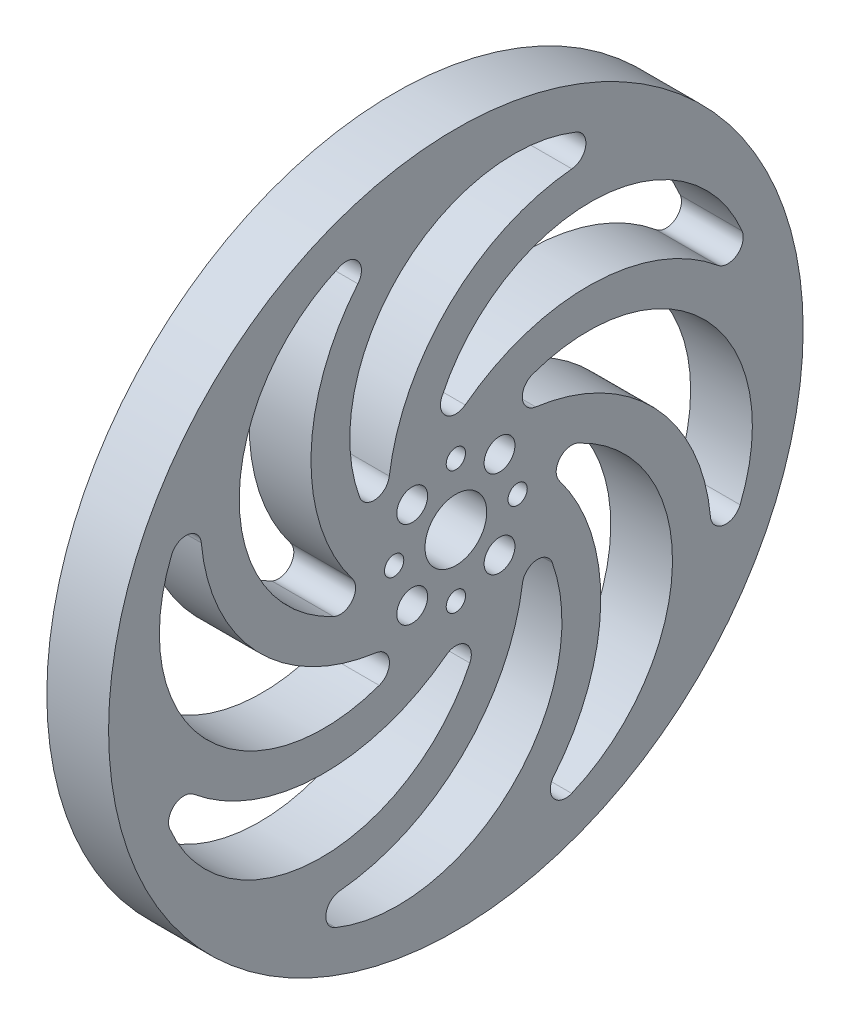
SolidWorks part; units mm, degrees
material "PMMA"
ref_plane "Front Plane" through (0, 0, 0) normal (0, 0, 1) x (1, 0, 0)
ref_plane "Top Plane" through (0, 0, 0) normal (0, 1, 0) x (1, 0, 0)
ref_plane "Right Plane" through (0, 0, 0) normal (1, 0, 0) x (0, 0, -1)
sketch "Sprocket" plane through (0, 0, 0) normal (1, 0, 0) x (0, 0, -1)
  circle A0 centre (0, 0) radius 45
  dimension "D1" = 90
extrude "Estrusione-Estrusione2" add sketch "Sprocket" along normal blind 8 contours A0
sketch "Schizzo1" plane through (0, 0, 0) normal (1, 0, 0) x (0, 0, -1)
  line L0 (0, 45) -> (0, -45) construction
  line L1 (31.8198, -31.8198) -> (-31.8198, 31.8198) construction
  line L2 (-31.8198, -31.8198) -> (31.8198, 31.8198) construction
  line L4 (-45, 0) -> (45, 0) construction
  circle A0 centre (0, 0) radius 4
  circle A1 centre (-5.6569, 5.6569) radius 2
  circle A2 centre (5.6569, 5.6569) radius 2
  circle A3 centre (0, 8) radius 1.25
  circle A4 centre (8, 0) radius 1.25
  circle A5 centre (-8, 0) radius 1.25
  circle A6 centre (0, -8) radius 1.25
  circle A7 centre (0, 0) radius 45 construction
  circle A8 centre (5.6569, -5.6569) radius 2
  circle A9 centre (-5.6569, -5.6569) radius 2
  point P5 (0, 0)
  point P8 (0, 0)
  point P15 (0, 0)
  point P16 (0, 0)
  point P36 (0, 0)
  dimension "D1" = 8
  dimension "D2" = 2.5
  dimension "D10" = 4
  dimension "D3" = 8
  dimension "D4" = 8
  dimension "D5" = 8
  dimension "D6" = 8
  dimension "D7" = 45
  dimension "D8" = 45
  dimension "D9" = 45
  dimension "D11" = 8
  dimension "D12" = 4
extrude "Taglio-Estrusione2" cut sketch "Schizzo1" along direction (1, 0, 0) on the side of the normal through all
sketch "Schizzo2" plane through (8, 0, 0) normal (1, 0, 0) x (0, 0, -1)
  line L0 (0, 0) -> (0, 15) construction
  line L1 (0, 0) -> (35.233, 14.2351) construction
  arc A0 (10.3368, 8.6249) -> (32.9876, -15.0314) centre (6.7868, -17.4465) cw
  arc A1 (32.9876, -15.0314) -> (36.8299, -15.606) centre (34.9792, -14.8478) ccw
  arc A2 (9.9294, 12.4885) -> (36.8299, -15.606) centre (17.1355, -7.5376) cw
  arc A3 (-1.8095, 15.8519) -> (1.2105, 13.4079) centre (0, 15) ccw
  arc A4 (33.9546, 12.697) -> (37.0778, 15.0076) centre (35.233, 14.2351) ccw
  circle A5 centre (0, 0) radius 15 construction
  circle A6 centre (0, 0) radius 38 construction
  circle A7 centre (0, 0) radius 45 construction
  arc A8 (1.2105, 13.4079) -> (33.9546, 12.697) centre (17.1355, -7.5376) cw
  arc A9 (9.9294, 12.4885) -> (10.3368, 8.6249) centre (10.6066, 10.6066) ccw
  arc A10 (13.4079, -1.2105) -> (12.697, -33.9546) centre (-7.5376, -17.1355) cw
  arc A11 (12.697, -33.9546) -> (15.0076, -37.0778) centre (14.2351, -35.233) ccw
  arc A12 (15.8519, 1.8095) -> (15.0076, -37.0778) centre (6.7868, -17.4465) cw
  arc A13 (15.8519, 1.8095) -> (13.4079, -1.2105) centre (15, 0) ccw
  arc A14 (8.6249, -10.3368) -> (-15.0314, -32.9876) centre (-17.4465, -6.7868) cw
  arc A15 (-15.0314, -32.9876) -> (-15.606, -36.8299) centre (-14.8478, -34.9792) ccw
  arc A16 (12.4885, -9.9294) -> (-15.606, -36.8299) centre (-7.5376, -17.1355) cw
  arc A17 (12.4885, -9.9294) -> (8.6249, -10.3368) centre (10.6066, -10.6066) ccw
  arc A18 (-1.8095, 15.8519) -> (37.0778, 15.0076) centre (17.4465, 6.7868) cw
  arc A19 (-1.2105, -13.4079) -> (-33.9546, -12.697) centre (-17.1355, 7.5376) cw
  arc A20 (-33.9546, -12.697) -> (-37.0778, -15.0076) centre (-35.233, -14.2351) ccw
  arc A21 (1.8095, -15.8519) -> (-37.0778, -15.0076) centre (-17.4465, -6.7868) cw
  arc A22 (1.8095, -15.8519) -> (-1.2105, -13.4079) centre (0, -15) ccw
  arc A23 (-10.3368, -8.6249) -> (-32.9876, 15.0314) centre (-6.7868, 17.4465) cw
  arc A24 (-32.9876, 15.0314) -> (-36.8299, 15.606) centre (-34.9792, 14.8478) ccw
  arc A25 (-9.9294, -12.4885) -> (-36.8299, 15.606) centre (-17.1355, 7.5376) cw
  arc A26 (-9.9294, -12.4885) -> (-10.3368, -8.6249) centre (-10.6066, -10.6066) ccw
  arc A27 (-13.4079, 1.2105) -> (-12.697, 33.9546) centre (7.5376, 17.1355) cw
  arc A28 (-12.697, 33.9546) -> (-15.0076, 37.0778) centre (-14.2351, 35.233) ccw
  arc A29 (-15.8519, -1.8095) -> (-15.0076, 37.0778) centre (-6.7868, 17.4465) cw
  arc A30 (-15.8519, -1.8095) -> (-13.4079, 1.2105) centre (-15, 0) ccw
  arc A31 (-8.6249, 10.3368) -> (15.0314, 32.9876) centre (17.4465, 6.7868) cw
  arc A32 (15.0314, 32.9876) -> (15.606, 36.8299) centre (14.8478, 34.9792) ccw
  arc A33 (-12.4885, 9.9294) -> (15.606, 36.8299) centre (7.5376, 17.1355) cw
  arc A34 (-12.4885, 9.9294) -> (-8.6249, 10.3368) centre (-10.6066, 10.6066) ccw
  point P41 (0, 0)
  point P50 (0, 0)
  point P76 (10.6066, 10.6066)
  point P90 (0, 0)
  dimension "D1" = 30
  dimension "D2" = 7
  dimension "D3" = 68
  dimension "D4" = 2
  dimension "D5" = 2
  dimension "D6" = 8
  dimension "D7" = 5.0289
extrude "Taglio-Estrusione3" cut sketch "Schizzo2" along direction (1, 0, 0) on the side against the normal through all
sketch "Schizzo3" plane through (0, 0, 0) normal (1, 0, 0) x (0, 0, -1)
  line L0 (0, 3) -> (0, 5) construction
  line L1 (2.958, -0.5) -> (4.3681, -0.5)
  line L2 (-0.5, 4.3681) -> (-0.5, 2.958)
  line L3 (0.5, 2.958) -> (0.5, 4.3681)
  line L4 (4.3681, 0.5) -> (2.958, 0.5)
  line L5 (-0.5, -2.958) -> (-0.5, -4.3681)
  line L6 (0.5, -4.3681) -> (0.5, -2.958)
  line L7 (-2.958, 0.5) -> (-4.3681, 0.5)
  line L8 (-4.3681, -0.5) -> (-2.958, -0.5)
  circle A0 centre (0, 0) radius 2
  circle A1 centre (0, 0) radius 3
  arc A3 (-0.5, 4.3681) -> (0.5, 4.3681) centre (0, 0) cw
  arc A4 (-0.5, 2.958) -> (0.5, 2.958) centre (0, 0) cw
  arc A5 (4.3681, 0.5) -> (4.3681, -0.5) centre (0, 0) cw
  arc A6 (2.958, 0.5) -> (2.958, -0.5) centre (0, 0) cw
  arc A7 (0.5, -4.3681) -> (-0.5, -4.3681) centre (0, 0) cw
  arc A8 (0.5, -2.958) -> (-0.5, -2.958) centre (0, 0) cw
  arc A9 (-4.3681, -0.5) -> (-4.3681, 0.5) centre (0, 0) cw
  arc A10 (-2.958, -0.5) -> (-2.958, 0.5) centre (0, 0) cw
  point P30 (0, 0)
  dimension "D1" = 4
  dimension "D2" = 6
  dimension "D3" = 0.5
  dimension "D5" = 4
  dimension "D4" = 0.5
extrude "Estrusione-Estrusione3" [suppressed] add sketch "Schizzo3" along normal blind 8 contours A5 L4 A1 L1 | A7 L6 A1 L5 | A9 L8 A1 L7 | A1 A4 A0
fillet "Raccordo1" [suppressed] radius 2
equation "\"Thickness8\"=8"
equation "\"D1@Estrusione-Estrusione2\"=\"Thickness8\""
equation "\"D\"=90"
equation "\"D1@Sprocket\"=\"D\""
equation "\"D4@Schizzo1\"=\"D3@Schizzo1\""
equation "\"D5@Schizzo1\"=\"D3@Schizzo1\""
equation "\"D6@Schizzo1\"=\"D3@Schizzo1\""
equation "\"D1@Estrusione-Estrusione3\"=\"Thickness8\""
